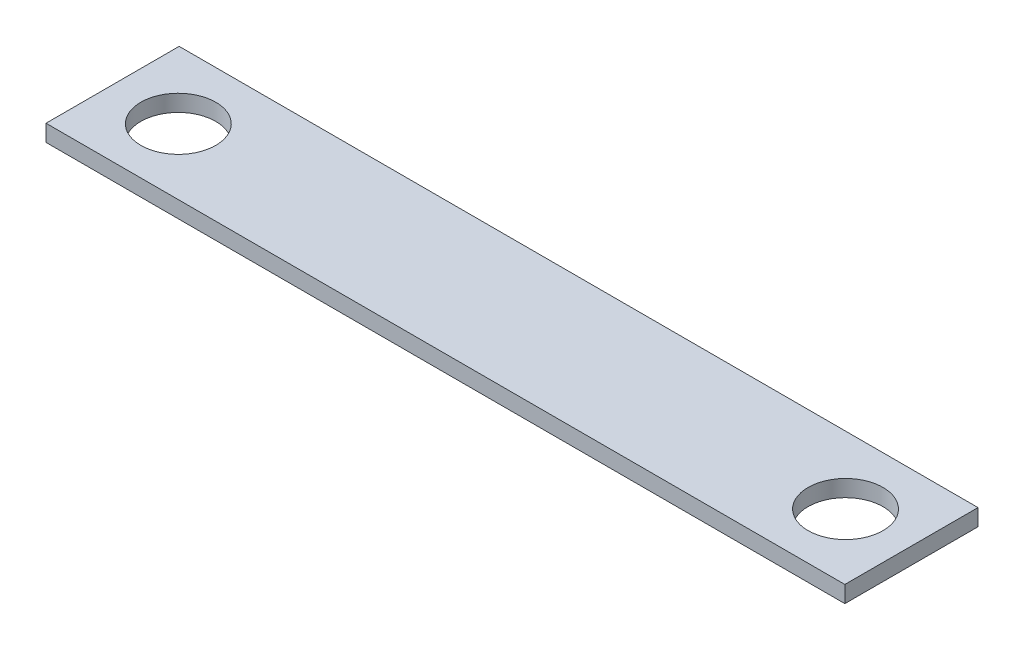
SolidWorks part; units mm, degrees
ref_plane "Front Plane" through (0, 0, 0) normal (0, 0, 1) x (1, 0, 0)
ref_plane "Top Plane" through (0, 0, 0) normal (0, 1, 0) x (1, 0, 0)
ref_plane "Right Plane" through (0, 0, 0) normal (1, 0, 0) x (0, 0, -1)
sketch "Sketch1" plane through (0, 0, 0) normal (0, 1, 0) x (1, 0, 0)
  line L1 (-137.8465, 47.7795) -> (166.9535, 47.7795)
  line L2 (-137.8465, 47.7795) -> (-137.8465, -3.0205)
  line L3 (-137.8465, -3.0205) -> (166.9535, -3.0205)
  line L4 (166.9535, 47.7795) -> (166.9535, -3.0205)
  dimension "D1" = 304.8
  dimension "D2" = 50.8
extrude "Boss-Extrude1" add sketch "Sketch1" along normal blind 6.35
sketch "Sketch2" plane through (0, 6.35, 0) normal (0, 1, 0) x (1, 0, 0)
  circle A0 centre (-112.4154, 22.0276) radius 14.2875
  circle A1 centre (142.1659, 22.0276) radius 14.2875
  dimension "D1" = 28.575
  dimension "D2" = 28.575
extrude "Cut-Extrude1" cut sketch "Sketch2" against normal blind 6.35
